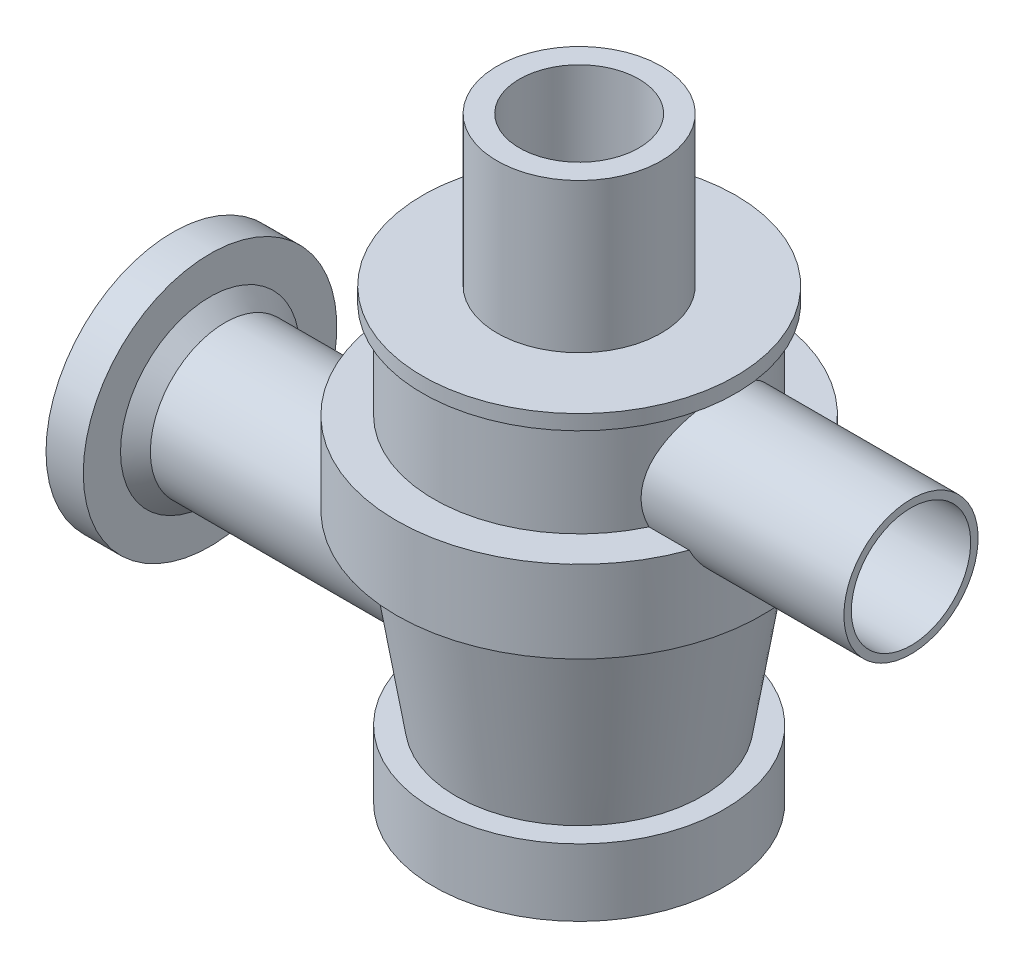
SolidWorks part; units mm, degrees
ref_plane "Front Plane" through (0, 0, 0) normal (0, 0, 1) x (1, 0, 0)
ref_plane "Top Plane" through (0, 0, 0) normal (0, 1, 0) x (1, 0, 0)
ref_plane "Right Plane" through (0, 0, 0) normal (1, 0, 0) x (0, 0, -1)
sketch "Sketch2" plane through (0, 0, 0) normal (0, 0, 1) x (1, 0, 0)
  line L0 (407.8333, 704) -> (2039.1667, 704) construction
  line L5 (133.2988, 67.0038) -> (137.7961, 67.0038)
  line L6 (98.2976, 77.001) -> (98.2976, 72.0043)
  line L8 (93.3009, 74.001) -> (95.2976, 74.001)
  line L11 (95.2976, 74.001) -> (95.2976, 70.762)
  line L12 (93.3009, 77.001) -> (98.2976, 77.001)
  line L13 (95.2976, 70.762) -> (99.0541, 67.0038)
  line L14 (99.0541, 67.0038) -> (133.2988, 67.0038)
  line L15 (93.3009, 60) -> (133.2988, 60) construction
  line L16 (98.2976, 72.0043) -> (100.2972, 70.0038)
  line L17 (93.3009, 77.001) -> (93.3009, 74.001)
  line L19 (100.2972, 70.0038) -> (137.7961, 70.0038)
  line L20 (100.2972, 70.0038) -> (133.2988, 70.0038) construction
  line L21 (137.7961, 70.0038) -> (137.7961, 67.0038)
  line L22 (133.2988, 60) -> (137.7961, 60) construction
  line L23 (93.3009, 60) -> (137.7961, 60) construction
  dimension "D1" = 3
revolve "Revolve2" add sketch "Sketch2" angle 360 about L15
sketch "Sketch3" plane through (0, 0, 0) normal (0, 0, 1) x (1, 0, 0)
  line L0 (93.3009, 60) -> (167.2916, 60) construction
  line L1 (164.296, 46.9956) -> (168.2966, 71.9906)
  line L2 (167.2916, 37.9928) -> (167.2916, 46.9956)
  line L3 (168.2966, 71.9906) -> (172.2878, 71.9906)
  line L4 (172.2878, 71.9906) -> (172.2878, 82.9952)
  line L5 (168.7961, 98.0297) -> (158.8005, 98.0297)
  line L6 (152.2873, 37.9928) -> (167.2916, 37.9928)
  line L7 (167.2916, 46.9956) -> (164.296, 46.9956)
  line L8 (149.2873, 31.9918) -> (149.2873, 40.9928)
  line L9 (149.2873, 40.9928) -> (164.2916, 40.9928)
  line L10 (164.2916, 40.9928) -> (164.2916, 43.9956)
  line L11 (172.2878, 82.9952) -> (167.2916, 82.9952)
  line L12 (147.792, 31.9918) -> (147.792, 120.2193) construction
  line L13 (167.2916, 82.9952) -> (167.2916, 95.9979)
  line L14 (164.2916, 43.9956) -> (161.1717, 43.9956)
  line L15 (165.6636, 74.9906) -> (169.2878, 74.9906)
  line L16 (167.2916, 95.9979) -> (168.7961, 96.0301)
  line L17 (152.2873, 31.9918) -> (152.2873, 37.9928)
  line L18 (169.2878, 74.9906) -> (169.2878, 79.9952)
  line L19 (168.7961, 96.0301) -> (168.7961, 98.0297)
  line L20 (169.2878, 79.9952) -> (164.2916, 79.9952)
  line L21 (158.8005, 98.0297) -> (158.8005, 118.0278)
  line L22 (164.2916, 79.9952) -> (164.2916, 95.0297)
  line L23 (164.2916, 95.0297) -> (164.2916, 95.0297)
  line L24 (164.2916, 95.0297) -> (164.2916, 95.0297)
  line L25 (164.2916, 95.0297) -> (155.8005, 95.0297)
  line L26 (155.8005, 95.0297) -> (155.8005, 118.0278)
  line L27 (155.8005, 118.0278) -> (158.8005, 118.0278)
  line L28 (149.2873, 31.9918) -> (152.2873, 31.9918)
  line L29 (161.1717, 43.9956) -> (165.6636, 74.9906)
  arc A4 (161.1717, 43.9956) -> (164.318, 60.6324) centre (208.4883, 43.6629) cw construction
  arc A5 (164.318, 60.6324) -> (165.6636, 74.9906) centre (324.7098, 52.8439) cw construction
  arc A6 (167.2916, 60) -> (168.2966, 71.9906) centre (324.7098, 52.8439) cw construction
  arc A7 (164.296, 46.9956) -> (167.2916, 60) centre (208.4883, 43.6629) cw construction
  dimension "D1" = 3
revolve "Revolve3" add sketch "Sketch3" angle 360 about L12
sketch "Sketch4" plane through (0, 0, 0) normal (0, 0, 1) x (1, 0, 0)
  line L0 (163.2854, 94.4934) -> (192.2872, 94.4934)
  line L2 (192.2872, 95.4934) -> (192.2872, 94.4934)
  line L4 (163.2854, 86.4931) -> (192.2872, 86.4931) construction
  line L5 (163.2854, 95.4934) -> (192.2872, 95.4934)
  line L6 (163.2854, 95.4934) -> (163.2854, 94.4934)
  dimension "D1" = 1
revolve "Revolve4" add sketch "Sketch4" angle 360 about L4
hole_wizard "M18x2.0 Tapped Hole1" positions "3DSketch11" profile "Sketch15" tap size "M18x2.0" standard "ANSI Metric"
sketch3d "3DSketch11"
  line L0 (192.2872, 86.4931, 0) -> (170.8414, 86.4931, 0) construction
  point P0 (192.2872, 86.4931, 0)
sketch "Sketch15" plane through (192.2872, 86.4931, 0) normal (0, 1, 0) x (0, 0, -1)
  line L0 (0, 0) -> (0, 27.9956)
  line L1 (0, 27.9956) -> (8, 27.9956)
  line L2 (8, 27.9956) -> (8, 0)
  line L5 (8, 0) -> (0, 0)
  line L11 (0, -6.35) -> (0, 107.95) construction
  dimension "Thru Tap Drill Dia." = 16
  dimension "Thru Tap Drill Depth" = 27.9956
hole_wizard "Ø12.0mm Dowel Hole1" positions "3DSketch23" profile "Sketch27" hole size "Ø12.0" standard "ANSI Metric"
sketch3d "3DSketch23"
  line L0 (95.2976, 60, 0) -> (99.0541, 60, 0) construction
  point P0 (95.2976, 60, 0)
sketch "Sketch27" plane through (95.2976, 60, 0) normal (0, 1, 0) x (0, 0, 1)
  line L0 (0, 0) -> (0, 36.7953)
  line L1 (0, 36.7953) -> (6, 36.7953)
  line L2 (6, 36.7953) -> (6, 0)
  line L5 (6, 0) -> (0, 0)
  line L11 (0, -6.35) -> (0, 107.95) construction
  dimension "Thru Hole Dia." = 12
  dimension "Thru Hole Depth" = 36.7953
